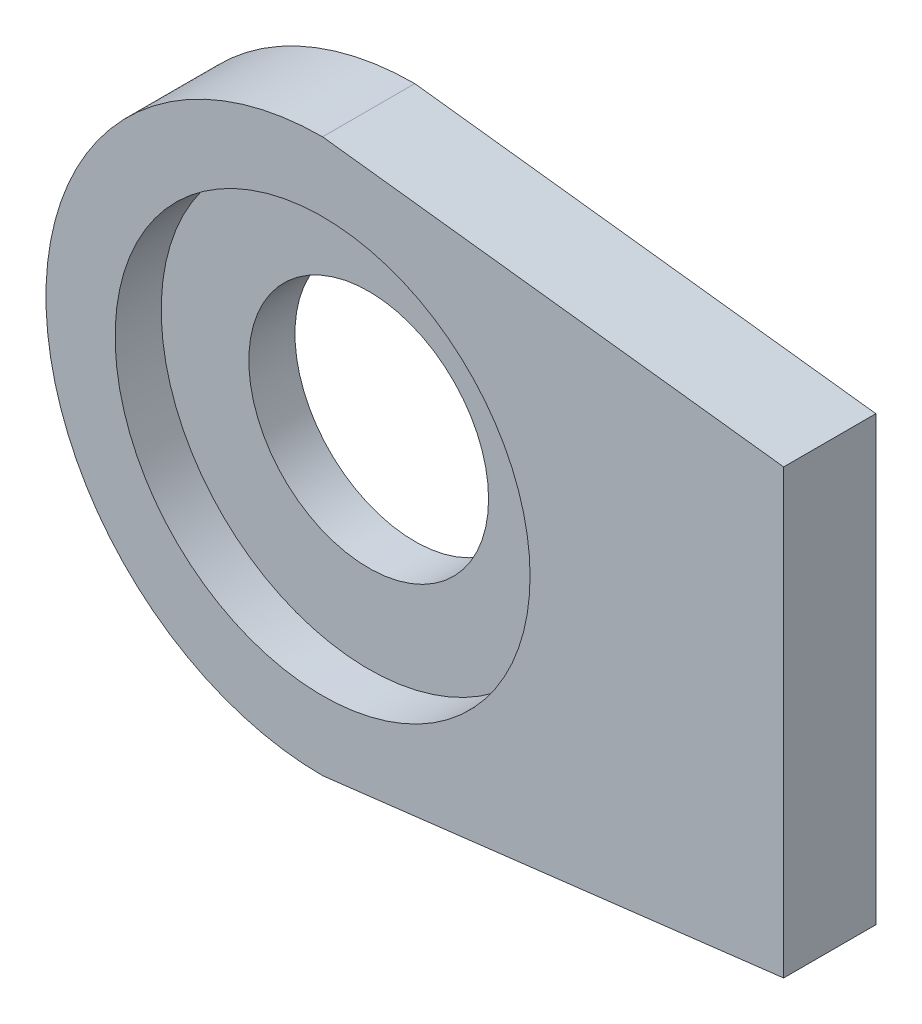
SolidWorks part; units mm, degrees
ref_plane "Front Plane" through (0, 0, 0) normal (0, 0, 1) x (1, 0, 0)
ref_plane "Top Plane" through (0, 0, 0) normal (0, 1, 0) x (1, 0, 0)
ref_plane "Right Plane" through (0, 0, 0) normal (1, 0, 0) x (0, 0, -1)
sketch "Sketch2" plane through (0, 0, 0) normal (0, 0, 1) x (1, 0, 0)
  line L2 (10, -4.8) -> (10, 4.8)
  line L3 (0, 6) -> (10, 4.8)
  line L4 (0, -6) -> (10, -4.8)
  arc A0 (0, 6) -> (0, -6) centre (0, 0) ccw
  point P1 (10, 0)
  dimension "D1" = 12
  dimension "D2" = 10
  dimension "D3" = 9.6
  dimension "D4" = 0
extrude "Boss-Extrude1" add sketch "Sketch2" along normal blind 2
sketch "Sketch5" plane through (0, 0, 2) normal (0, 0, 1) x (1, 0, 0)
  circle A0 centre (0, 0) radius 2.6
extrude "Cut-Extrude1" cut sketch "Sketch5" against normal blind 2
sketch "Sketch6" plane through (0, 0, 2) normal (0, 0, 1) x (1, 0, 0)
  circle A0 centre (0, 0) radius 4.5
extrude "Cut-Extrude2" cut sketch "Sketch6" against normal blind 1
